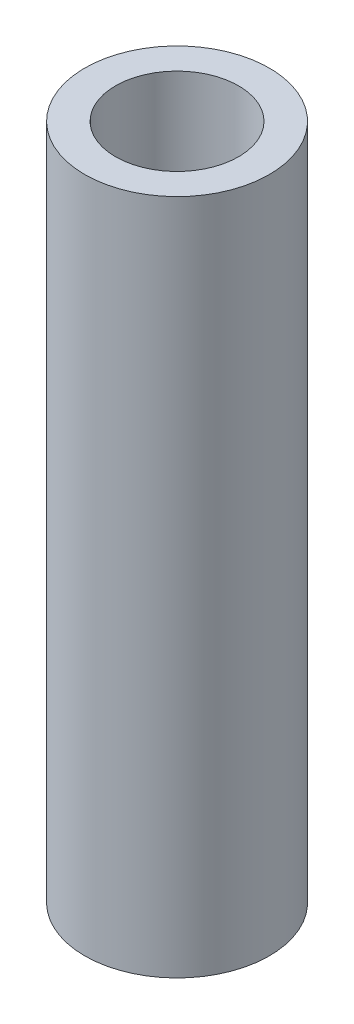
SolidWorks part; units mm, degrees
material "ABS"
ref_plane "Спереди" through (0, 0, 0) normal (0, 0, 1) x (1, 0, 0)
ref_plane "Сверху" through (0, 0, 0) normal (0, 1, 0) x (1, 0, 0)
ref_plane "Справа" through (0, 0, 0) normal (1, 0, 0) x (0, 0, -1)
sketch "Эскиз1" plane through (0, 0, 0) normal (0, 1, 0) x (1, 0, 0)
  circle A2 centre (0, 0) radius 2
  circle A3 centre (0, 0) radius 3
  dimension "D1" = 6
  dimension "D2" = 4
extrude "Бобышка-Вытянуть1" add sketch "Эскиз1" along normal blind 22
